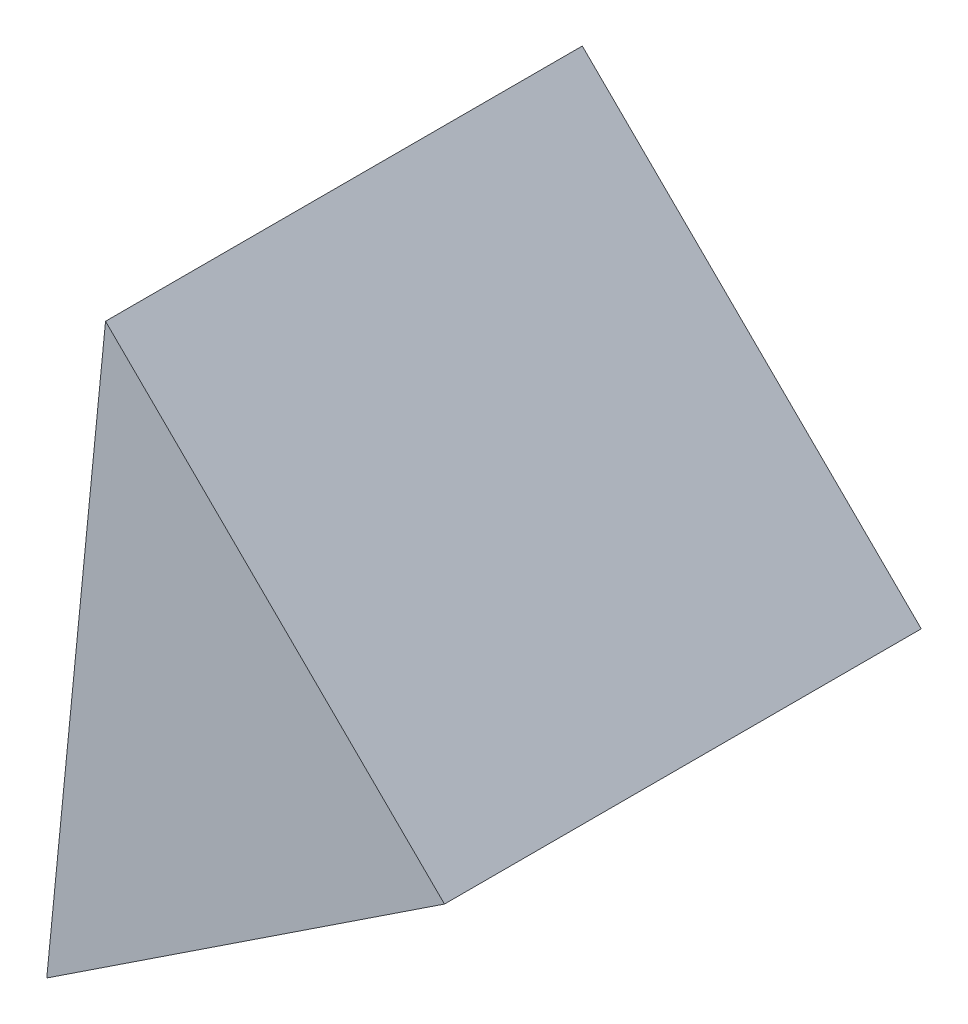
SolidWorks part; units mm, degrees
ref_plane "前视基准面" through (0, 0, 0) normal (0, 0, 1) x (1, 0, 0)
ref_plane "上视基准面" through (0, 0, 0) normal (0, 1, 0) x (1, 0, 0)
ref_plane "右视基准面" through (0, 0, 0) normal (1, 0, 0) x (0, 0, -1)
sketch "草图2" plane through (0, 0, 0) normal (0, 0, 1) x (1, 0, 0)
  line L0 (4.8574, 3.6045) -> (1.3025, 7.1206)
  line L1 (4.8574, 3.6045) -> (0.6862, 0.8475)
  line L2 (0.6862, 0.8475) -> (1.3025, 7.1206)
  dimension "D1" = 5
  dimension "D2" = 5
extrude "凸台-拉伸1" add sketch "草图2" along normal blind 5
